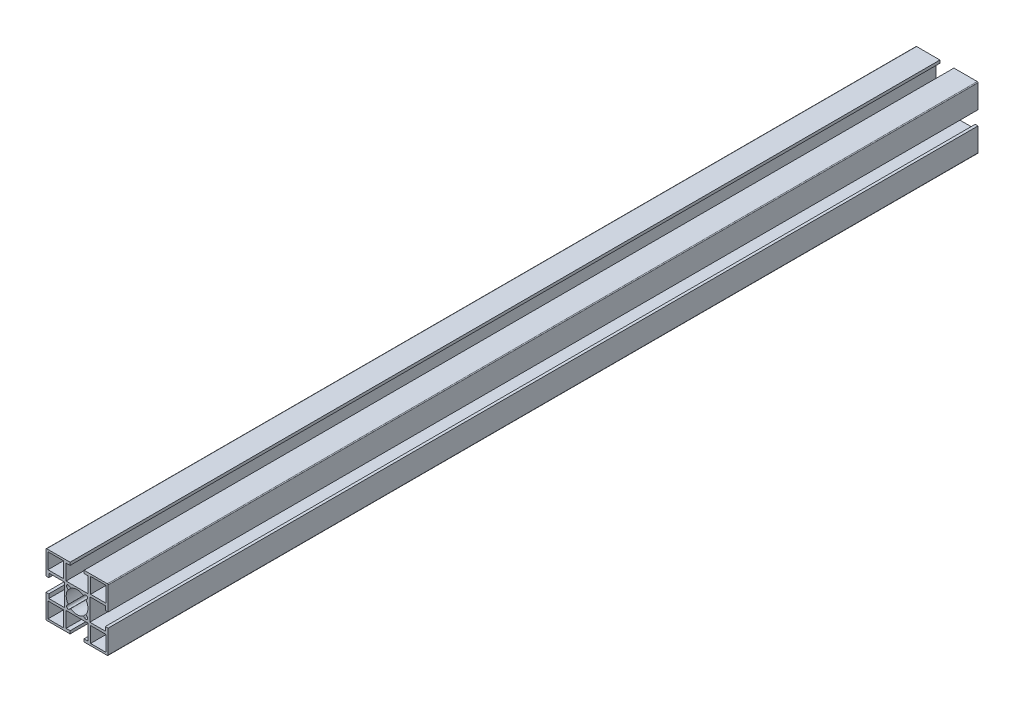
SolidWorks part; units mm, degrees
ref_plane "前视基准面" through (0, 0, 0) normal (0, 0, 1) x (1, 0, 0)
ref_plane "上视基准面" through (0, 0, 0) normal (0, 1, 0) x (1, 0, 0)
ref_plane "右视基准面" through (0, 0, 0) normal (1, 0, 0) x (0, 0, -1)
other "Configuration Table"
sketch "草图1" plane through (0, 0, 0) normal (1, 0, 0) x (0, 0, -1)
  line L0 (0, 0) -> (560, 0)
  dimension "D1" = 560
other "铝型材 40 X 40A X R0.5(1)"
ref_plane "基准面1" through (0, 0, 0) normal (0, 0, -1) x (0, 1, 0)
sketch "Sketch1" plane through (0, 0, 0) normal (0, 0, -1) x (0, 1, 0)
  line L0 (0, 0) -> (0, 16.3773) construction
  line L1 (0, 0) -> (-5.6569, 5.6569) construction
  line L2 (-19.5, 20) -> (-4.5, 20)
  line L3 (-20, 19.5) -> (-20, 4.5)
  line L4 (-19.5, -20) -> (-4.5, -20)
  line L5 (20, 19.5) -> (20, 4.5)
  line L6 (-4.879, 6.4347) -> (-4.1104, 5.6661)
  line L7 (-6.4347, 4.879) -> (-5.6661, 4.1104)
  line L8 (6.4347, 4.879) -> (5.6661, 4.1104)
  line L9 (0, 0) -> (20, 0) construction
  line L10 (4.879, 6.4347) -> (4.1104, 5.6661)
  line L11 (4.879, -6.4347) -> (4.1104, -5.6661)
  line L12 (6.4347, -4.879) -> (5.6661, -4.1104)
  line L13 (-6.4347, -4.879) -> (-5.6661, -4.1104)
  line L14 (-4.879, -6.4347) -> (-4.1104, -5.6661)
  line L15 (-4.5, 20) -> (-4.5, 18.2)
  line L16 (-18.7, 18.7) -> (-8.7, 18.7)
  line L17 (-18.7, 18.7) -> (-18.7, 8.7)
  line L18 (-18.7, 8.7) -> (-8.7, 8.7)
  line L19 (-8.7, 18.7) -> (-8.7, 8.7)
  line L20 (-7.1, 18.2) -> (-4.5, 18.2)
  line L21 (-7.1, 18.2) -> (-7.1, 8.2)
  line L22 (-7.1, 8.2) -> (7.1, 8.2)
  line L23 (7.1, 18.2) -> (7.1, 8.2)
  line L24 (4.5, 20) -> (4.5, 18.2)
  line L25 (4.5, 20) -> (19.5, 20)
  line L26 (4.5, 18.2) -> (7.1, 18.2)
  line L27 (8.7, 18.7) -> (8.7, 8.7)
  line L28 (18.7, 8.7) -> (8.7, 8.7)
  line L29 (18.7, 18.7) -> (18.7, 8.7)
  line L30 (18.7, 18.7) -> (8.7, 18.7)
  line L31 (18.2, 7.1) -> (8.2, 7.1)
  line L32 (18.2, 7.1) -> (18.2, 4.5)
  line L33 (20, 4.5) -> (18.2, 4.5)
  line L34 (8.2, 7.1) -> (8.2, -7.1)
  line L35 (18.2, -7.1) -> (8.2, -7.1)
  line L36 (18.2, -4.5) -> (18.2, -7.1)
  line L37 (20, -4.5) -> (18.2, -4.5)
  line L38 (7.1, -18.2) -> (7.1, -8.2)
  line L39 (7.1, -18.2) -> (4.5, -18.2)
  line L40 (4.5, -20) -> (4.5, -18.2)
  line L41 (7.1, -8.2) -> (-7.1, -8.2)
  line L42 (-7.1, -18.2) -> (-7.1, -8.2)
  line L43 (-4.5, -18.2) -> (-7.1, -18.2)
  line L44 (-4.5, -20) -> (-4.5, -18.2)
  line L45 (-18.2, -7.1) -> (-8.2, -7.1)
  line L46 (-18.2, -7.1) -> (-18.2, -4.5)
  line L47 (-20, -4.5) -> (-18.2, -4.5)
  line L48 (-8.2, -7.1) -> (-8.2, 7.1)
  line L49 (-18.2, 7.1) -> (-8.2, 7.1)
  line L50 (-18.2, 4.5) -> (-18.2, 7.1)
  line L51 (-20, 4.5) -> (-18.2, 4.5)
  line L52 (4.5, -20) -> (19.5, -20)
  line L53 (-20, -4.5) -> (-20, -19.5)
  line L54 (20, -4.5) -> (20, -19.5)
  line L55 (18.7, -18.7) -> (18.7, -8.7)
  line L56 (18.7, -8.7) -> (8.7, -8.7)
  line L57 (8.7, -18.7) -> (8.7, -8.7)
  line L58 (18.7, -18.7) -> (8.7, -18.7)
  line L59 (-8.7, -18.7) -> (-8.7, -8.7)
  line L60 (-18.7, -8.7) -> (-8.7, -8.7)
  line L61 (-18.7, -18.7) -> (-8.7, -18.7)
  line L62 (-18.7, -18.7) -> (-18.7, -8.7)
  arc A0 (-4.1104, 5.6661) -> (4.1104, 5.6661) centre (0, 0) cw
  arc A1 (-4.879, 6.4347) -> (-6.4347, 4.879) centre (-5.6569, 5.6569) ccw
  arc A2 (-4.1104, -5.6661) -> (4.1104, -5.6661) centre (0, 0) ccw
  arc A3 (-5.6661, 4.1104) -> (-5.6661, -4.1104) centre (0, 0) ccw
  arc A4 (6.4347, 4.879) -> (4.879, 6.4347) centre (5.6569, 5.6569) ccw
  arc A5 (4.879, -6.4347) -> (6.4347, -4.879) centre (5.6569, -5.6569) ccw
  arc A6 (-6.4347, -4.879) -> (-4.879, -6.4347) centre (-5.6569, -5.6569) ccw
  arc A7 (5.6661, 4.1104) -> (5.6661, -4.1104) centre (0, 0) cw
  arc A8 (-19.5, 20) -> (-20, 19.5) centre (-19.5, 19.5) ccw
  arc A9 (19.5, 20) -> (20, 19.5) centre (19.5, 19.5) cw
  arc A10 (19.5, -20) -> (20, -19.5) centre (19.5, -19.5) ccw
  arc A11 (-20, -19.5) -> (-19.5, -20) centre (-19.5, -19.5) ccw
  point P86 (20, 20)
  point P87 (-20, 20)
  point P88 (-20, -20)
  point P89 (20, -20)
  point P90 (0, 0)
  dimension "D2" = 7
  dimension "D3" = 45
  dimension "D4" = 1.1
  dimension "D5" = 1.8
  dimension "D6" = 8
  dimension "D7" = 1.3
  dimension "D8" = 14.2
  dimension "D10" = 10
  dimension "D11" = 10
  dimension "D12" = 40
  dimension "D13" = 9
  dimension "D14" = 0.5
  dimension "D9" = 1.3
